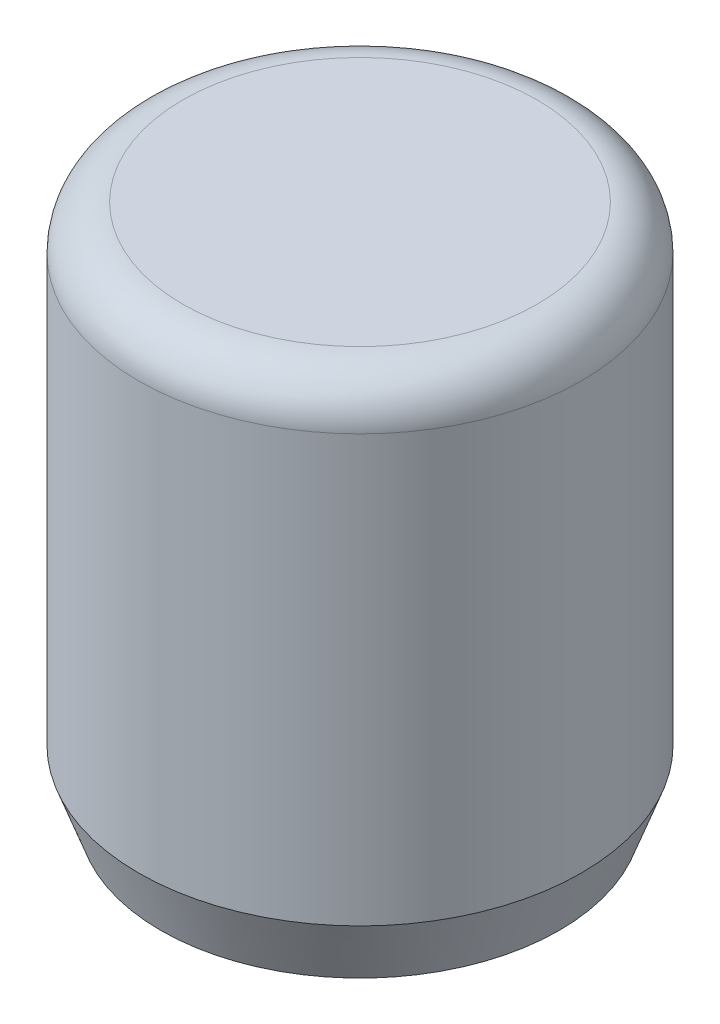
SolidWorks part; units mm, degrees
ref_plane "Спереди" through (0, 0, 0) normal (0, 0, 1) x (1, 0, 0)
ref_plane "Сверху" through (0, 0, 0) normal (0, 1, 0) x (1, 0, 0)
ref_plane "Справа" through (0, 0, 0) normal (1, 0, 0) x (0, 0, -1)
sketch "Sketch1" plane through (0, 0, 0) normal (0, 1, 0) x (1, 0, 0)
  circle A0 centre (0, 0) radius 5
  dimension "D1" = 10
extrude "Boss-Extrude1" add sketch "Sketch1" along normal blind 12
sketch "Sketch2" plane through (0, 0, 0) normal (0, -1, 0) x (1, 0, 0)
  circle A0 centre (0, 0) radius 3
  dimension "D1" = 6
extrude "Cut-Extrude1" cut sketch "Sketch2" against normal blind 6
fillet "Fillet1" radius 1 1 edges at (0, 12, 5)
chamfer "Chamfer1" distance 0.5 angle 70 1 edges at (0, 0, 5)
